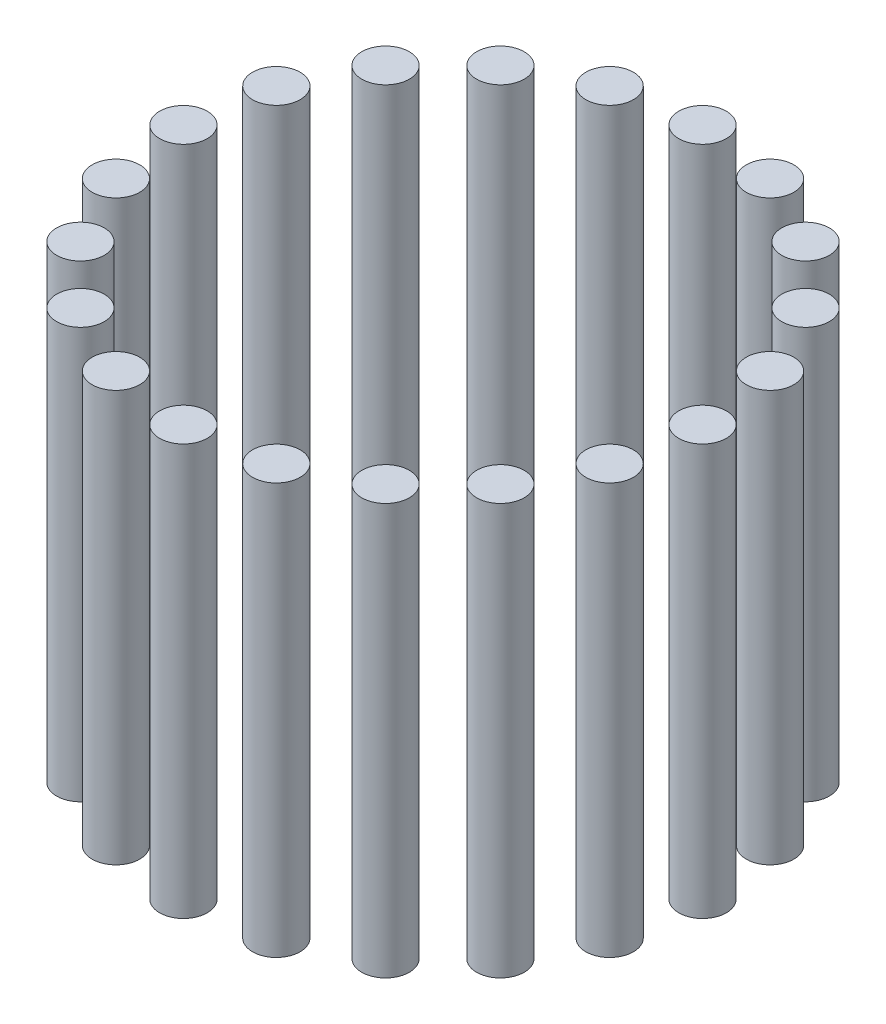
SolidWorks part; units mm, degrees
ref_plane "Front Plane" through (0, 0, 0) normal (0, 0, 1) x (1, 0, 0)
ref_plane "Top Plane" through (0, 0, 0) normal (0, 1, 0) x (1, 0, 0)
ref_plane "Right Plane" through (0, 0, 0) normal (1, 0, 0) x (0, 0, -1)
sketch "Sketch1" plane through (0, 0, 0) normal (0, 1, 0) x (1, 0, 0)
  circle A0 centre (0, 0) radius 60
  circle A1 centre (-60, 0) radius 5.5
  circle A2 centre (-57.0634, 18.541) radius 5.5
  circle A3 centre (-48.541, 35.2671) radius 5.5
  circle A4 centre (-35.2671, 48.541) radius 5.5
  circle A5 centre (-18.541, 57.0634) radius 5.5
  circle A6 centre (0, 60) radius 5.5
  circle A7 centre (18.541, 57.0634) radius 5.5
  circle A8 centre (35.2671, 48.541) radius 5.5
  circle A9 centre (48.541, 35.2671) radius 5.5
  circle A10 centre (57.0634, 18.541) radius 5.5
  circle A11 centre (60, 0) radius 5.5
  circle A12 centre (57.0634, -18.541) radius 5.5
  circle A13 centre (48.541, -35.2671) radius 5.5
  circle A14 centre (35.2671, -48.541) radius 5.5
  circle A15 centre (18.541, -57.0634) radius 5.5
  circle A16 centre (0, -60) radius 5.5
  circle A17 centre (-18.541, -57.0634) radius 5.5
  circle A18 centre (-35.2671, -48.541) radius 5.5
  circle A19 centre (-48.541, -35.2671) radius 5.5
  circle A20 centre (-57.0634, -18.541) radius 5.5
  point P45 (0, 0)
extrude "Boss-Extrude1" add sketch "Sketch1" along normal blind 95 contours A0 A2 | A1 | A20 | A3 | A4 | A5 | A6 | A7 | A8 | A9 | A10 | A11 | A12 | A13 | A14 | A15 | A16 | A17 | A18 | A19
